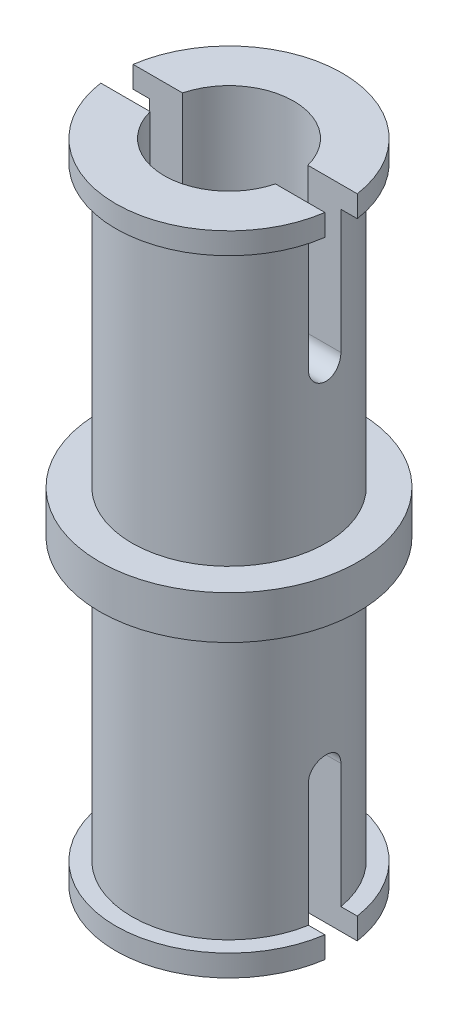
SolidWorks part; units mm, degrees
ref_plane "Front Plane" through (0, 0, 0) normal (0, 0, 1) x (1, 0, 0)
ref_plane "Top Plane" through (0, 0, 0) normal (0, 1, 0) x (1, 0, 0)
ref_plane "Right Plane" through (0, 0, 0) normal (1, 0, 0) x (0, 0, -1)
sketch "Sketch1" plane through (0, 0, 0) normal (0, 1, 0) x (1, 0, 0)
  circle A0 centre (0, 0) radius 1
  circle A1 centre (0, 0) radius 1.5
  point P5 (0, 0)
  dimension "D1" = 3
  dimension "D2" = 2
extrude "Boss-Extrude1" add sketch "Sketch1" along normal blind 5
sketch "Sketch2" plane through (0, 5, 0) normal (0, 1, 0) x (1, 0, 0)
  circle A0 centre (0, 0) radius 1
  circle A1 centre (0, 0) radius 2
  dimension "D1" = 4
extrude "Boss-Extrude2" add sketch "Sketch2" against normal blind 0.3333
sketch "Sketch3" plane through (0, 0, 0) normal (0, -1, 0) x (-1, 0, 0)
  circle A0 centre (0, 0) radius 1.75
  circle A1 centre (0, 0) radius 1
  dimension "D1" = 3.5
extrude "Boss-Extrude4" add sketch "Sketch3" against normal blind 0.3333
sketch "Sketch4" plane through (0, 0, 0) normal (1, 0, 0) x (0, 0, -1)
  line L1 (0.25, 0) -> (-0.25, 0)
  line L2 (0.25, 0) -> (0.25, 2.25)
  line L3 (0.25, 2.25) -> (-0.25, 2.25)
  line L4 (-0.25, 0) -> (-0.25, 2.25)
  circle A0 centre (0, 2.25) radius 0.25
  point P7 (0, 0)
  dimension "D1" = 0.5
  dimension "D2" = 2.25
extrude "Cut-Extrude1" cut sketch "Sketch4" against normal through all both and the other way through all contours L3 A0
mirror "Mirror1" about plane through (0, 5, 0) normal (0, 1, 0) of bodies 105
